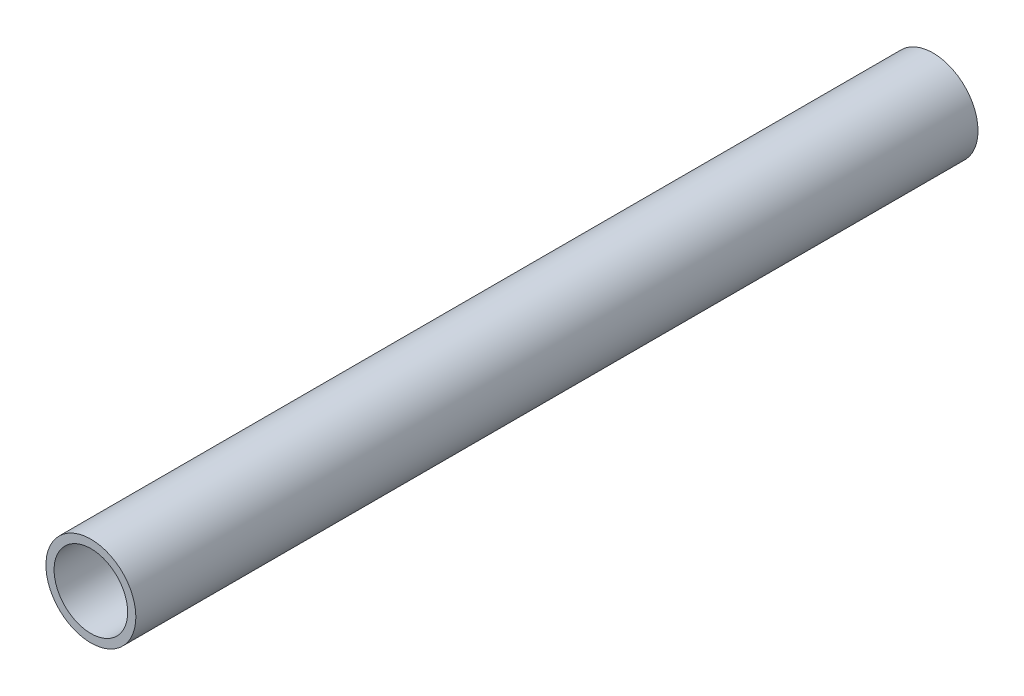
SolidWorks part; units mm, degrees
ref_plane "Ön Düzlem" through (0, 0, 0) normal (0, 0, 1) x (1, 0, 0)
ref_plane "Üst Düzlem" through (0, 0, 0) normal (0, 1, 0) x (1, 0, 0)
ref_plane "Sağ Düzlem" through (0, 0, 0) normal (1, 0, 0) x (0, 0, -1)
sketch "Sketch1" plane through (0, 0, 0) normal (0, 0, 1) x (1, 0, 0)
  circle A0 centre (0, 0) radius 5.5
  circle A1 centre (0, 0) radius 4.5
  dimension "D1" = 9
  dimension "D2" = 1
extrude "Boss-Extrude1" add sketch "Sketch1" along normal blind 103
